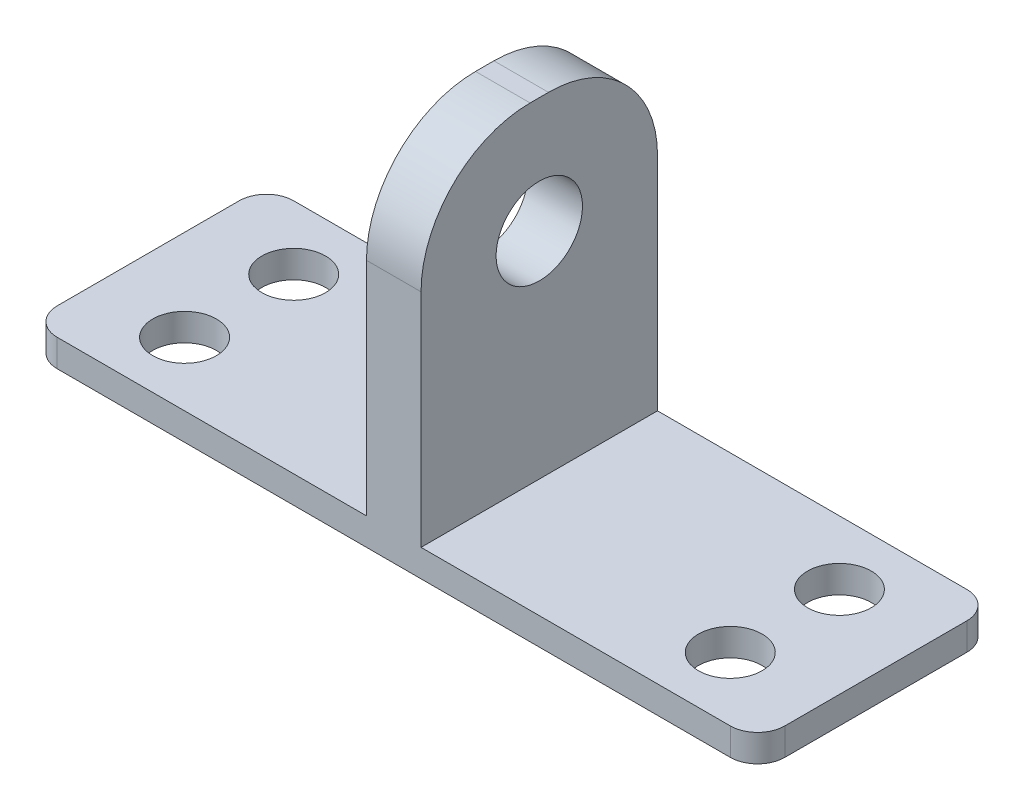
SolidWorks part; units mm, degrees
ref_plane "Front Plane" through (0, 0, 0) normal (0, 0, 1) x (1, 0, 0)
ref_plane "Top Plane" through (0, 0, 0) normal (0, 1, 0) x (1, 0, 0)
ref_plane "Right Plane" through (0, 0, 0) normal (1, 0, 0) x (0, 0, -1)
sketch "Sketch1" plane through (0, 0, 0) normal (0, 1, 0) x (1, 0, 0)
  line L0 (0, -26) -> (80, -26)
  line L1 (80, -26) -> (80, 0)
  line L2 (80, 0) -> (0, 0)
  line L3 (0, 0) -> (0, -26)
  line L4 (40, -26) -> (40, 0) construction
  line L5 (0, -13) -> (80, -13) construction
  circle A0 centre (10, -19) radius 3.5
  circle A1 centre (10, -7) radius 3.5
  circle A2 centre (70, -7) radius 3.5
  circle A3 centre (70, -19) radius 3.5
  dimension "D1" = 80
  dimension "D6" = 7
  dimension "D2" = 26
  dimension "D4" = 10
  dimension "D5" = 7
  dimension "D7" = 7
extrude "Boss-Extrude1" add sketch "Sketch1" along normal blind 3
fillet "Fillet1" radius 2.9972 4 edges at (80, 1.5, 26) (0, 1.5, 26) (0, 1.5, 0) (80, 1.5, 0)
sketch "Sketch2" plane through (0, 3, 0) normal (0, 1, 0) x (1, 0, 0)
  line L0 (40, 0) -> (40, -26) construction
  line L1 (77.0028, 0) -> (2.9972, 0) construction
  line L2 (2.9972, -26) -> (77.0028, -26) construction
  line L3 (43, 0) -> (40, 0)
  line L4 (40, 0) -> (37, 0)
  line L5 (43, 0) -> (43, -26)
  line L6 (37, 0) -> (37, -26)
  line L7 (37, -26) -> (40, -26)
  line L8 (40, -26) -> (43, -26)
  dimension "D1" = 6
extrude "Boss-Extrude2" add sketch "Sketch2" along normal blind 36.322 contours L8 L5 L3 L4 L6 L7
fillet "Fillet2" radius 11.9888 2 edges at (40, 39.322, 26) (40, 39.322, 0)
sketch "Sketch3" plane through (37, 0, 0) normal (-1, 0, 0) x (0, 0, 1)
  line L0 (13, 39.322) -> (13, 0) construction
  line L1 (11.9888, 39.322) -> (14.0112, 39.322) construction
  line L2 (2.9972, 0) -> (23.0028, 0) construction
  circle A0 centre (13, 26.622) radius 4.75
  dimension "D1" = 12.7
  dimension "D2" = 9.5
extrude "Cut-Extrude1" cut sketch "Sketch3" against normal up to next contours A0
